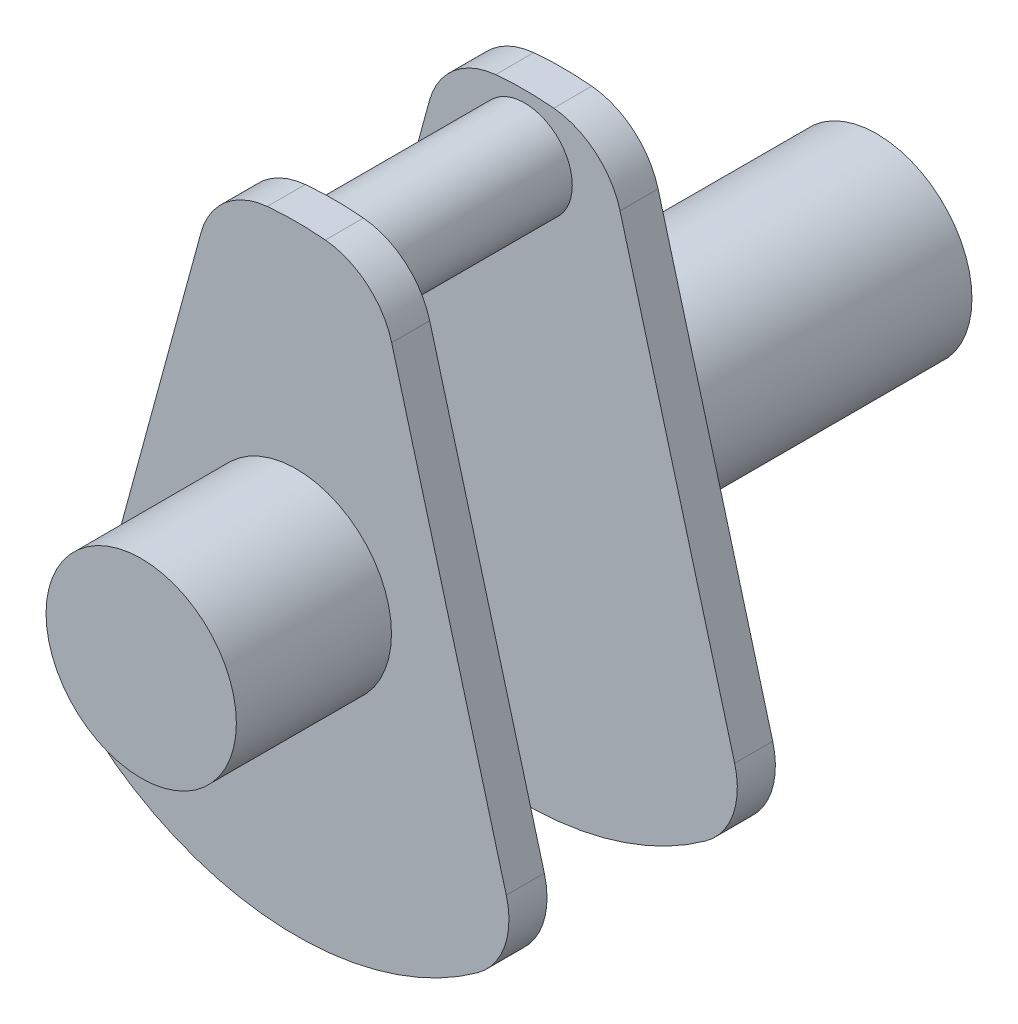
SolidWorks part; units mm, degrees
ref_plane "Front Plane" through (0, 0, 0) normal (0, 0, 1) x (1, 0, 0)
ref_plane "Top Plane" through (0, 0, 0) normal (0, 1, 0) x (1, 0, 0)
ref_plane "Right Plane" through (0, 0, 0) normal (1, 0, 0) x (0, 0, -1)
sketch "Sketch1" plane through (0, 0, 0) normal (0, 0, 1) x (1, 0, 0)
  line L0 (0, 6.5) -> (0, -6.5) construction
  line L1 (-2.0038, 5.2985) -> (-4.4127, -3.5522)
  line L2 (2.0038, 5.2985) -> (4.4127, -3.5522)
  arc A0 (-3.8056, -5.2695) -> (3.8056, -5.2695) centre (0, 0) ccw
  arc A1 (0.6102, 6.4713) -> (-0.6102, 6.4713) centre (0, 0) ccw
  arc A2 (2.0038, 5.2985) -> (0.6102, 6.4713) centre (0.46, 4.8784) ccw
  arc A3 (-2.0038, 5.2985) -> (-0.6102, 6.4713) centre (-0.46, 4.8784) cw
  arc A4 (4.4127, -3.5522) -> (3.8056, -5.2695) centre (2.8688, -3.9724) cw
  arc A5 (-4.4127, -3.5522) -> (-3.8056, -5.2695) centre (-2.8688, -3.9724) ccw
  point P10 (1.7415, 6.2624)
  point P13 (-1.7415, 6.2624)
  point P16 (4.675, -4.516)
  point P19 (-4.675, -4.516)
  dimension "D1" = 13
  dimension "D4" = 1.6
  dimension "D5" = 1.6
  dimension "D2" = 30.45
  dimension "D3" = 0.92
extrude "Boss-Extrude1" add sketch "Sketch1" along normal blind 0.8
sketch "Sketch2" plane through (0, 0, 0.8) normal (0, 0, 1) x (1, 0, 0)
  line L0 (0, 6.5) -> (0, 5.26) construction
  arc A2 (0.6102, 6.4713) -> (-0.6102, 6.4713) centre (0, 0) ccw construction
  circle A3 centre (0, 5.26) radius 1
  dimension "D1" = 2
  dimension "D2" = 5.26
extrude "Boss-Extrude2" add sketch "Sketch2" along normal blind 2
sketch "Sketch3" plane through (0, 0, 0) normal (0, 0, -1) x (-1, 0, 0)
  circle A0 centre (0, 0) radius 2
  dimension "D1" = 4
extrude "Boss-Extrude3" add sketch "Sketch3" along normal blind 3.26
mirror "Mirror1" about plane through (0, 5.26, 2.8) normal (0, 0, 1) of bodies 103
sketch "Sketch4" plane through (0, 0, -3.26) normal (0, 0, -1) x (-1, 0, 0)
  circle A1 centre (0, 0) radius 2
  circle A2 centre (0, 0) radius 2
  dimension "D1" = 0
extrude "Boss-Extrude4" add sketch "Sketch4" along normal blind 3.34
sketch "Sketch5" plane through (0, 0, 0) normal (0, 0, -1) x (-1, 0, 0)
  line L0 (0, 0) -> (0, 5.5221) construction
  line L2 (0, 2.5193) -> (0.1, 2.5193)
  line L3 (0, 2.5193) -> (0, 2.0193)
  line L4 (0, 2.0193) -> (0.1, 2.0193)
  line L5 (0.1, 2.5193) -> (0.1, 2.0193)
  point P7 (0.1, 2.0483)
  point P8 (0.1, 2.0193)
  dimension "D1" = 0.1
  dimension "D2" = 0.5
extrude "Cut-Extrude1" cut sketch "Sketch5" against normal blind 0.1
